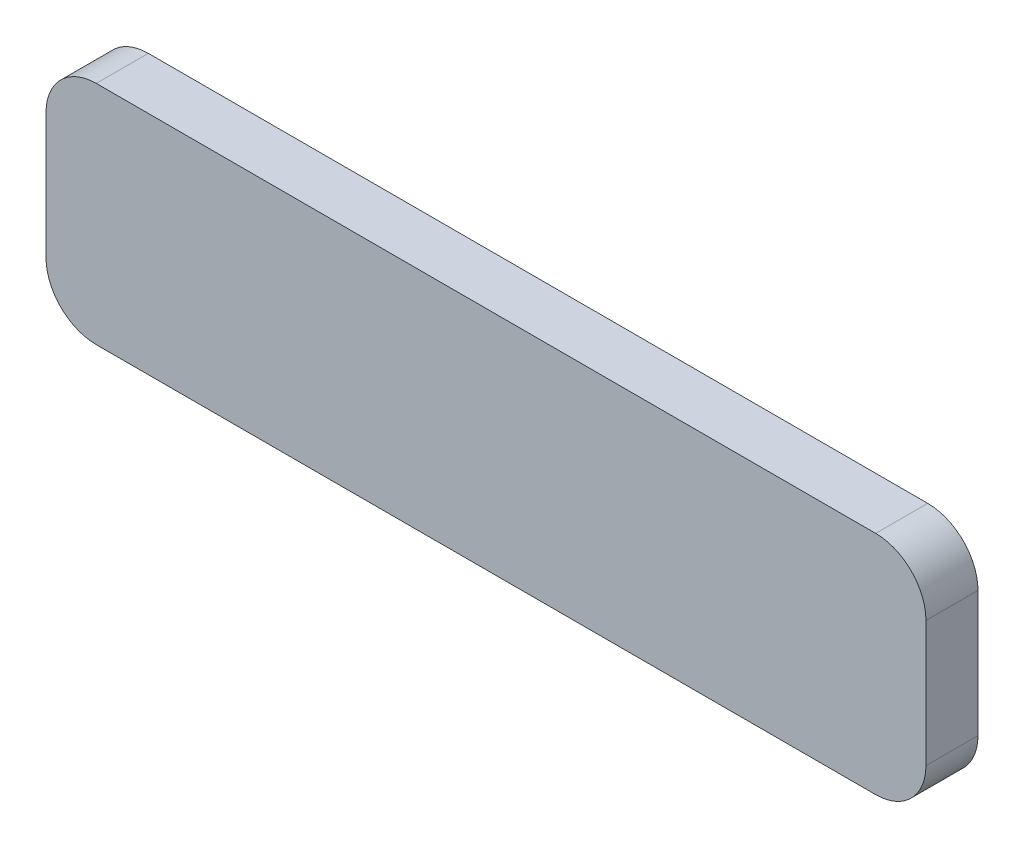
SolidWorks part; units mm, degrees
ref_plane "Front Plane" through (0, 0, 0) normal (0, 0, 1) x (1, 0, 0)
ref_plane "Top Plane" through (0, 0, 0) normal (0, 1, 0) x (1, 0, 0)
ref_plane "Right Plane" through (0, 0, 0) normal (1, 0, 0) x (0, 0, -1)
sketch "Sketch1" plane through (0, 0, 0) normal (0, 0, 1) x (1, 0, 0)
  line L1 (-44.45, -11.43) -> (44.45, -11.43)
  line L2 (-44.45, -11.43) -> (-44.45, 11.43)
  line L3 (-44.45, 11.43) -> (44.45, 11.43)
  line L4 (44.45, -11.43) -> (44.45, 11.43)
  line L5 (-44.45, -11.43) -> (44.45, 11.43) construction
  line L6 (-44.45, 11.43) -> (44.45, -11.43) construction
  point P0 (0, 0)
  dimension "D1" = 88.9
  dimension "D2" = 22.86
extrude "Boss-Extrude1" add sketch "Sketch1" along normal blind 5.2578
fillet "Fillet1" radius 5.08 1 edges at (-44.45, 11.43, 2.6289)
fillet "Fillet2" radius 5.08 1 edges at (44.45, 11.43, 2.6289)
fillet "Fillet3" radius 5.08 1 edges at (44.45, -11.43, 2.6289)
fillet "Fillet4" radius 5.08 1 edges at (-44.45, -11.43, 2.6289)
equation "\"Acrylic\"=\"Acrylic@Bumper.assembly\""
equation "\"D1@Boss-Extrude1\"=\"Acrylic\""
equation "\"D1@Sketch1\" = \"BumperWidth@Bumper_short.assembly\"+1"
